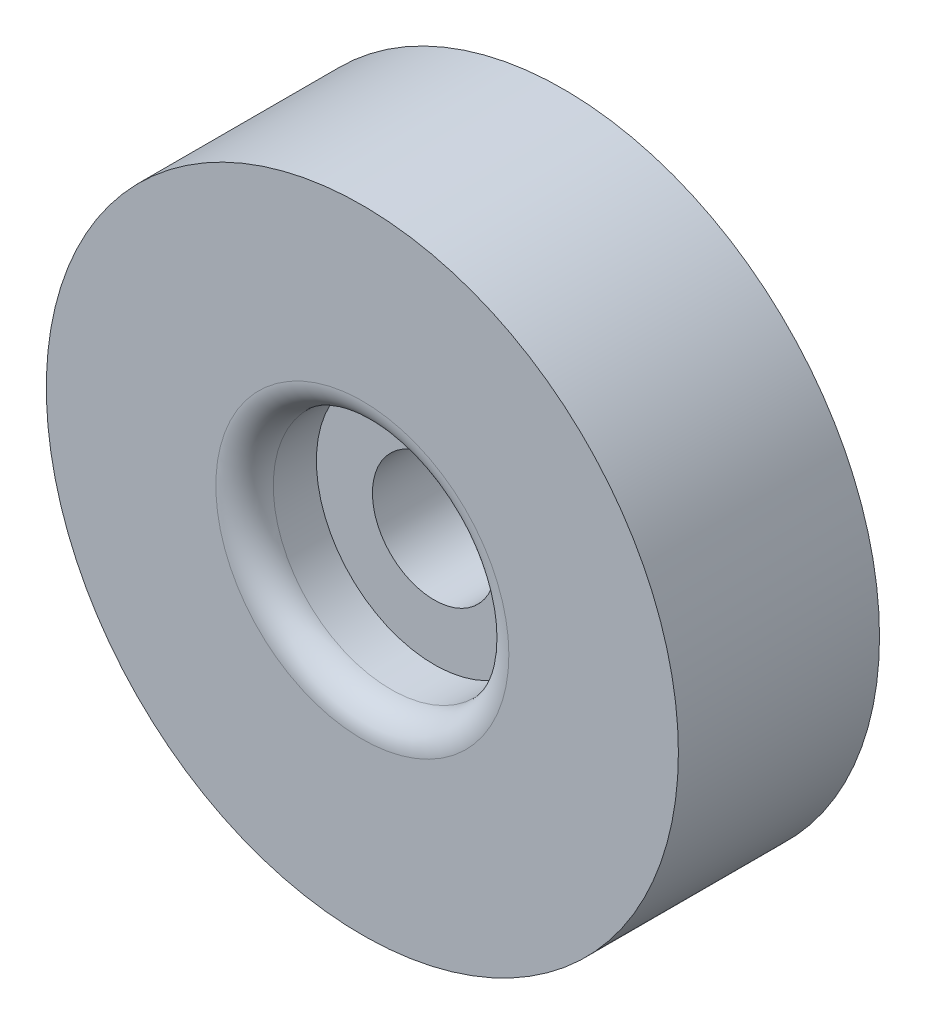
SolidWorks part; units mm, degrees
ref_plane "前视基准面" through (0, 0, 0) normal (0, 0, 1) x (1, 0, 0)
ref_plane "上视基准面" through (0, 0, 0) normal (0, 1, 0) x (1, 0, 0)
ref_plane "右视基准面" through (0, 0, 0) normal (1, 0, 0) x (0, 0, -1)
other "Configuration Table"
sketch "Sketch1" plane through (0, 0, 0) normal (0, 0, 1) x (1, 0, 0)
  circle A0 centre (0, 0) radius 11
  dimension "D1" = 22
extrude "Boss-Extrude1" add sketch "Sketch1" along normal blind 7
sketch "Sketch2" plane through (0, 0, 7) normal (0, 0, 1) x (1, 0, 0)
  circle A0 centre (0, 0) radius 4.1
  dimension "D1" = 8.2
extrude "Cut-Extrude1" cut sketch "Sketch2" against normal blind 2.5
sketch "Sketch3" plane through (0, 0, 4.5) normal (0, 0, 1) x (1, 0, 0)
  circle A0 centre (0, 0) radius 2.15
  dimension "D1" = 4.3
extrude "Cut-Extrude2" cut sketch "Sketch3" against normal through all
fillet "Fillet1" radius 1 1 edges at (4.1, 0, 7)
